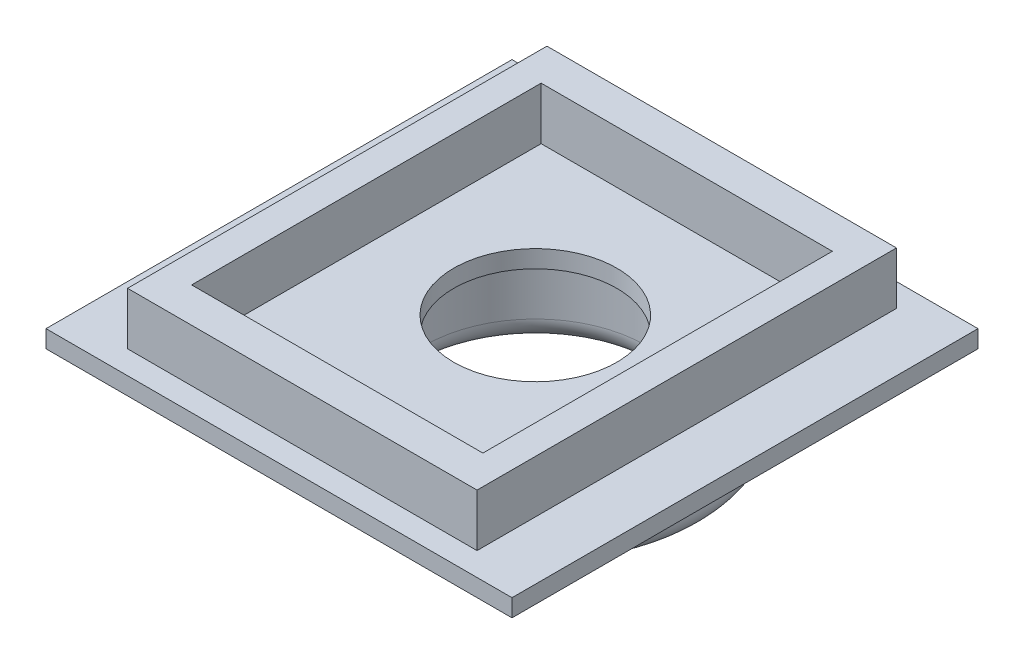
SolidWorks part; units mm, degrees
ref_plane "Alzado" through (0, 0, 0) normal (0, 0, 1) x (1, 0, 0)
ref_plane "Planta" through (0, 0, 0) normal (0, 1, 0) x (1, 0, 0)
ref_plane "Vista lateral" through (0, 0, 0) normal (1, 0, 0) x (0, 0, -1)
sketch "Croquis1" plane through (0, 0, 0) normal (0, 1, 0) x (1, 0, 0)
  line L1 (-20, -20) -> (20, -20)
  line L2 (-20, -20) -> (-20, 20)
  line L3 (-20, 20) -> (20, 20)
  line L4 (20, -20) -> (20, 20)
  line L5 (-20, -20) -> (20, 20) construction
  line L6 (-20, 20) -> (20, -20) construction
  point P0 (0, 0)
  dimension "D1" = 40
  dimension "D2" = 40
extrude "Saliente-Extruir1" add sketch "Croquis1" along normal blind 1.5
sketch "Croquis2" plane through (0, 1.5, 0) normal (0, 1, 0) x (1, 0, 0)
  line L0 (20, 20) -> (-20, 20) construction
  circle A0 centre (0, 2) radius 7
  dimension "D1" = 14
  dimension "D2" = 18
extrude "Cortar-Extruir1" cut sketch "Croquis2" against normal blind 1.5
sketch "Croquis3" plane through (0, 1.5, 0) normal (0, 1, 0) x (1, 0, 0)
  line L1 (-15, -18) -> (15, -18)
  line L2 (-15, -18) -> (-15, 18)
  line L3 (-15, 18) -> (15, 18)
  line L4 (15, -18) -> (15, 18)
  line L5 (-15, -18) -> (15, 18) construction
  line L6 (-15, 18) -> (15, -18) construction
  line L7 (-12.5, -15) -> (12.5, -15)
  line L8 (-12.5, -15) -> (-12.5, 15)
  line L9 (-12.5, 15) -> (12.5, 15)
  line L10 (12.5, -15) -> (12.5, 15)
  line L11 (-12.5, -15) -> (12.5, 15) construction
  line L12 (-12.5, 15) -> (12.5, -15) construction
  point P0 (0, 0)
  point P6 (0, 0)
  dimension "D1" = 36
  dimension "D2" = 30
  dimension "D3" = 3
extrude "Saliente-Extruir2" add sketch "Croquis3" along normal blind 4.5
sketch "Croquis4" plane through (0, 0, 0) normal (0, -1, 0) x (1, 0, 0)
  circle A0 centre (0, -2) radius 14.5
  circle A1 centre (0, -2) radius 9.5
  dimension "D1" = 29
  dimension "D2" = 5
extrude "Saliente-Extruir3" add sketch "Croquis4" along normal blind 7.5
fillet "Redondeo1" radius 2 2 edges at (0, -7.5, -11.5) (0, -7.5, -16.5)
